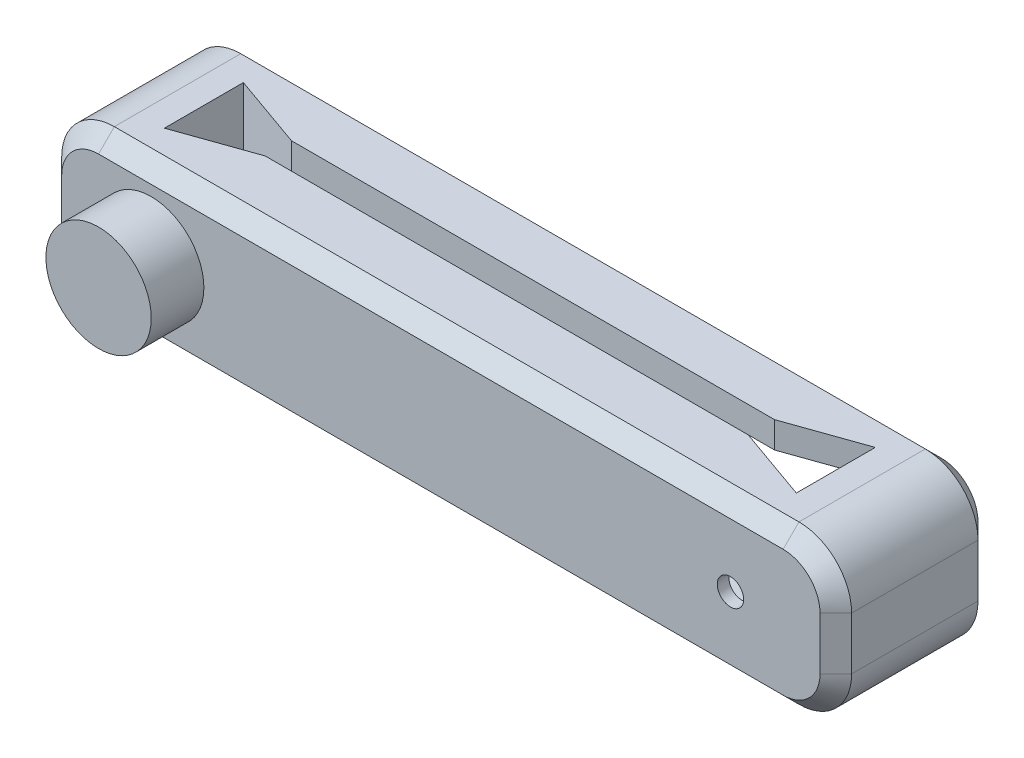
SolidWorks part; units mm, degrees
ref_plane "Front Plane" through (0, 0, 0) normal (0, 0, 1) x (1, 0, 0)
ref_plane "Top Plane" through (0, 0, 0) normal (0, 1, 0) x (1, 0, 0)
ref_plane "Right Plane" through (0, 0, 0) normal (1, 0, 0) x (0, 0, -1)
sketch "Sketch1" plane through (0, 0, 0) normal (0, 0, 1) x (1, 0, 0)
  line L1 (-75, 15) -> (75, 15)
  line L2 (-75, 15) -> (-75, -15)
  line L3 (-75, -15) -> (75, -15)
  line L4 (75, 15) -> (75, -15)
  line L5 (-75, 15) -> (75, -15) construction
  line L6 (-75, -15) -> (75, 15) construction
  point P0 (0, 0)
  dimension "D1" = 150
  dimension "D2" = 30
extrude "Boss-Extrude1" add sketch "Sketch1" along normal blind 30
sketch "Sketch2" plane through (0, 0, 30) normal (0, 0, 1) x (1, 0, 0)
  line L0 (-75, 15) -> (-75, -15) construction
  circle A0 centre (-55, 0) radius 10
  dimension "D2" = 20
  dimension "D1" = 20
extrude "Boss-Extrude2" add sketch "Sketch2" along normal blind 10
fillet "Fillet1" radius 10 4 edges at (-75, -15, 15) (-75, 15, 15) (75, -15, 15) (75, 15, 15)
sketch "Sketch3" plane through (0, 0, 0) normal (0, 0, -1) x (-1, 0, 0)
  line L0 (65, -15) -> (-65, -15) construction
  line L1 (-65, 10) -> (-25, 10)
  line L2 (-65, 10) -> (-65, -10)
  line L3 (-65, -10) -> (-25, -10)
  line L4 (-25, 10) -> (-25, -10)
  line L5 (-65, 10) -> (-25, -10) construction
  line L6 (-65, -10) -> (-25, 10) construction
  line L7 (-75, -5) -> (-75, 5) construction
  point P0 (-45, 0)
  dimension "D1" = 20
  dimension "D2" = 40
  dimension "D3" = 5
  dimension "D4" = 10
extrude "Cut-Extrude1" cut sketch "Sketch3" against normal blind 27.8
sketch "Sketch4" plane through (0, 0, 27.8) normal (0, 0, -1) x (-1, 0, 0)
  line L0 (-25, -10) -> (-25, 10) construction
  circle A0 centre (-55, 0) radius 2.5
  dimension "D1" = 5
  dimension "D2" = 30
extrude "Cut-Extrude2" cut sketch "Sketch4" against normal blind 27.8
sketch "Sketch5" plane through (0, 15, 0) normal (0, 1, 0) x (1, 0, 0)
  line L0 (-60, -7.5) -> (-60, -22.5)
  line L1 (-60, -22.5) -> (-45.8579, -17.5)
  line L2 (-45.8579, -17.5) -> (45.8579, -17.5)
  line L3 (45.8579, -17.5) -> (60, -22.5)
  line L4 (60, -22.5) -> (60, -7.5)
  line L5 (60, -7.5) -> (45.8579, -12.5)
  line L6 (45.8579, -12.5) -> (-45.8579, -12.5)
  line L7 (-45.8579, -12.5) -> (-60, -7.5)
  line L8 (65, -30) -> (-65, -30) construction
  line L10 (75, 0) -> (75, -30) construction
  line L12 (-75, -30) -> (-75, 0) construction
  dimension "D1" = 15
  dimension "D2" = 15
  dimension "D3" = 5
  dimension "D4" = 15
  dimension "D5" = 15
  dimension "D6" = 15
  dimension "D7" = 15
  dimension "D8" = 7.5
  dimension "D9" = 7.5
  dimension "D10" = 15
  dimension "D11" = 15
extrude "Cut-Extrude3" cut sketch "Sketch5" against normal through all
chamfer "Chamfer1" distance 3 angle 45 16 edges at (0, -15, 0) (72.0711, -12.0711, 0) (-72.0711, -12.0711, 0) (75, 0, 0) (-75, 0, 0) (72.0711, 12.0711, 0) (-72.0711, 12.0711, 0) (0, 15, 0) (0, -15, 30) (72.0711, -12.0711, 30) (-72.0711, -12.0711, 30) (75, 0, 30) (-75, 0, 30) (72.0711, 12.0711, 30) (-72.0711, 12.0711, 30) (0, 15, 30)
